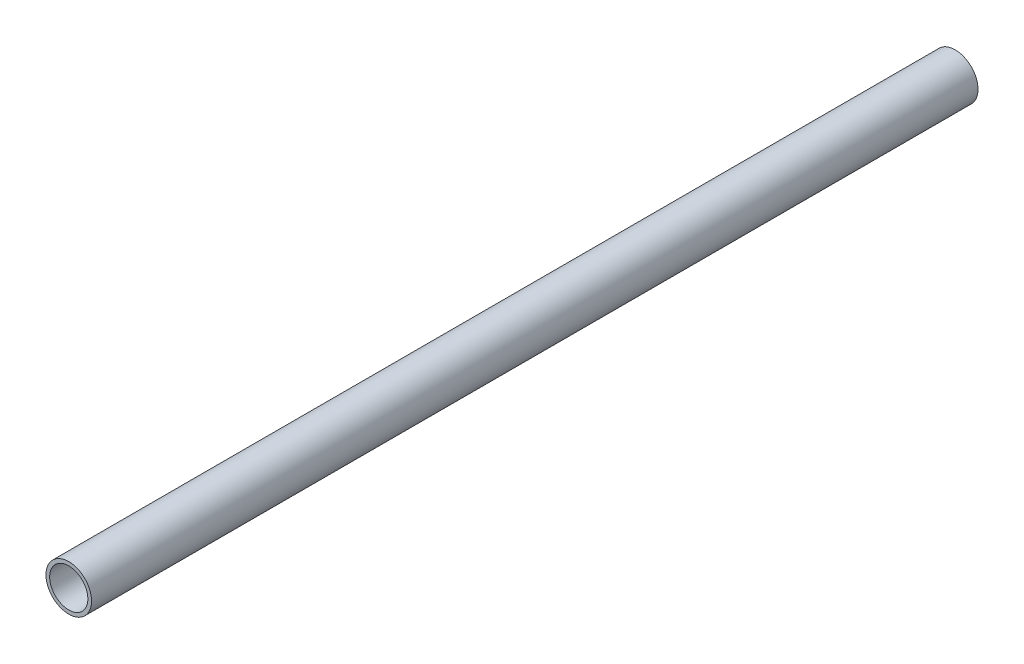
SolidWorks part; units mm, degrees
material "carbon"
ref_plane "Płaszczyzna XY" through (0, 0, 0) normal (0, 0, 1) x (1, 0, 0)
ref_plane "Płaszczyzna XZ" through (0, 0, 0) normal (0, 1, 0) x (1, 0, 0)
ref_plane "Płaszczyzna YZ" through (0, 0, 0) normal (1, 0, 0) x (0, 0, -1)
sketch "Szkic1" plane through (0, 0, 0) normal (0, 0, 1) x (1, 0, 0)
  circle A0 centre (0, 0) radius 7
  circle A1 centre (0, 0) radius 8.35
  dimension "D1" = 14
  dimension "D2" = 16.7
extrude "Dodanie-wyciągnięcie1" add sketch "Szkic1" along normal blind 315 and the other way up to surface (9.7177 mm away)
